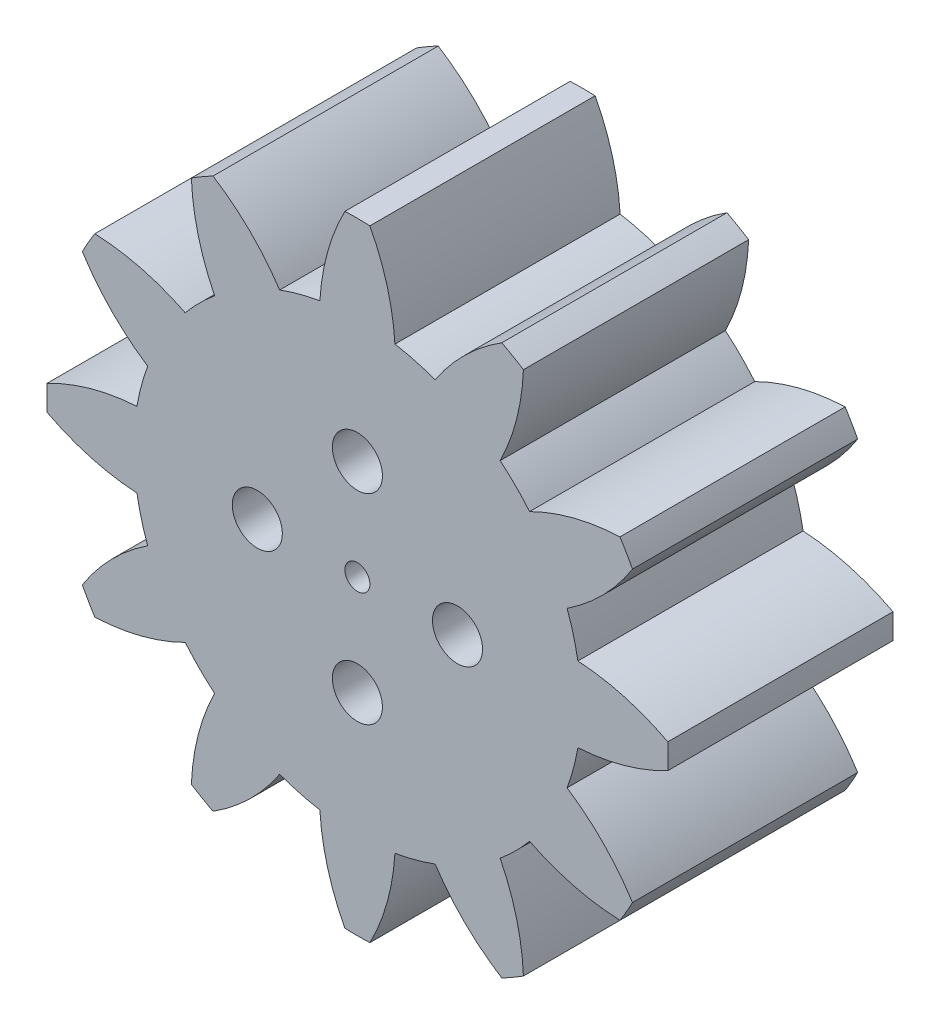
SolidWorks part; units mm, degrees
ref_plane "前视基准面" through (0, 0, 0) normal (0, 0, 1) x (1, 0, 0)
ref_plane "上视基准面" through (0, 0, 0) normal (0, 1, 0) x (1, 0, 0)
ref_plane "右视基准面" through (0, 0, 0) normal (1, 0, 0) x (0, 0, -1)
sketch "草图1" plane through (0, 0, 0) normal (0, 0, 1) x (1, 0, 0)
  line L0 (0, 24.83) -> (0, 0) construction
  arc A0 (3, 17.6215) -> (-3, 17.6215) centre (0, 0) ccw
  circle A1 centre (0, 0) radius 4.875 construction
  arc A140 (3, 17.6215) -> (1, 24.8096) centre (-14.7599, 16.5523) ccw
  arc A141 (1, 24.8096) -> (-1, 24.8096) centre (0, 0.355) ccw
  arc A142 (-1, 24.8096) -> (-3, 17.6215) centre (14.7599, 16.5523) ccw
  dimension "D1" = 35.75
  dimension "D2" = 24.475
  dimension "D3" = 9.75
  dimension "D4" = 6
  dimension "D5" = 2
extrude "凸台-拉伸1" add sketch "草图1" along normal blind 18
sketch "草图2" plane through (0, 0, 0) normal (0, 0, 1) x (1, 0, 0)
  circle A0 centre (0, 0) radius 17.875
  circle A1 centre (0, 0) radius 1
  dimension "D1" = 2
extrude "凸台-拉伸2" add sketch "草图2" along normal up to surface (18 mm away) up to face at (0, 21.337, 18)
pattern_circular "阵列(圆周)3" count 12 over 360 about axis through (0, 0, 0) along (0, 0, 1) of "凸台-拉伸1"
sketch "草图3" plane through (0, 0, 0) normal (0, 0, -1) x (-1, 0, 0)
  circle A0 centre (0, 0) radius 8 construction
  circle A1 centre (0, 8) radius 1.1
  dimension "D1" = 16
  dimension "D2" = 2.2
extrude "切除-拉伸1" cut sketch "草图3" against normal through all
pattern_circular "阵列(圆周)4" count 4 over 360 about axis through (0, 0, 0) along (0, 0, 1) of "切除-拉伸1"
sketch "草图4" plane through (0, 0, 18) normal (0, 0, 1) x (1, 0, 0)
  circle A0 centre (0, 8) radius 2
  circle A1 centre (8, 0) radius 2
  circle A2 centre (0, -8) radius 2
  circle A3 centre (-8, 0) radius 2
  dimension "D1" = 4
extrude "切除-拉伸2" cut sketch "草图4" against normal blind 10
